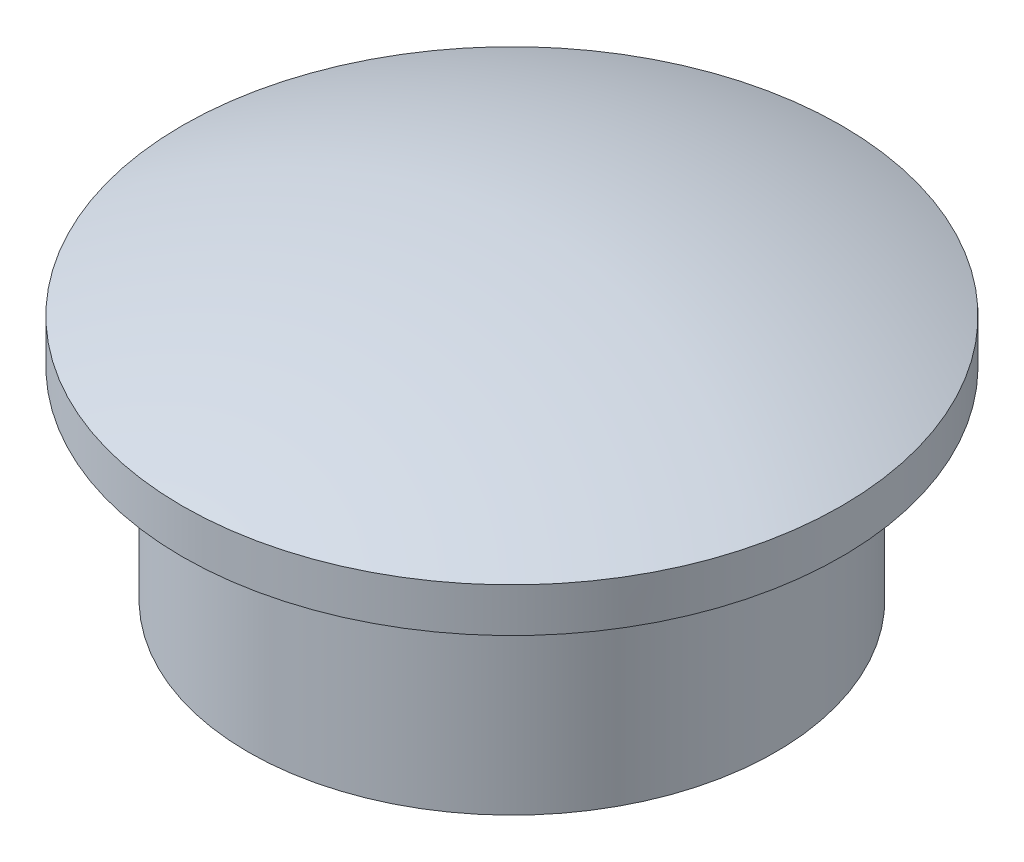
SolidWorks part; units mm, degrees
material "ABS"
ref_plane "Front Plane" through (0, 0, 0) normal (0, 0, 1) x (1, 0, 0)
ref_plane "Top Plane" through (0, 0, 0) normal (0, 1, 0) x (1, 0, 0)
ref_plane "Right Plane" through (0, 0, 0) normal (1, 0, 0) x (0, 0, -1)
sketch "Sketch1" plane through (0, 0, 0) normal (0, 1, 0) x (1, 0, 0)
  circle A0 centre (0, 0) radius 7.5
extrude "Boss-Extrude1" add sketch "Sketch1" along normal blind 1 contours A0
sketch "Sketch2" plane through (0, 0, 0) normal (0, 0, 1) x (1, 0, 0)
  line L1 (0, 2.55) -> (0, 0)
  line L2 (7.5, 1) -> (-7.5, 1) construction
  line L3 (7.5, 1) -> (-7.5, 1)
  arc A0 (-7.5, 1) -> (7.5, 1) centre (0, -16.3702) cw
  point P7 (0, 2.55)
  dimension "D1" = 2.55
revolve "Revolve1" add sketch "Sketch2" angle 360 about L1
sketch "Sketch4" plane through (0, 0, 0) normal (0, -1, 0) x (1, 0, 0)
  circle A0 centre (0, 0) radius 6
extrude "Boss-Extrude2" add sketch "Sketch4" along normal blind 4.6
sketch "Sketch5" plane through (0, -4.6, 0) normal (0, -1, 0) x (1, 0, 0)
  circle A0 centre (0, 0) radius 4.95
  dimension "D1" = 9.9
extrude "Cut-Extrude1" cut sketch "Sketch5" against normal blind 5.6
equation "\"D1@Sketch2\"=7.15-4.6"
